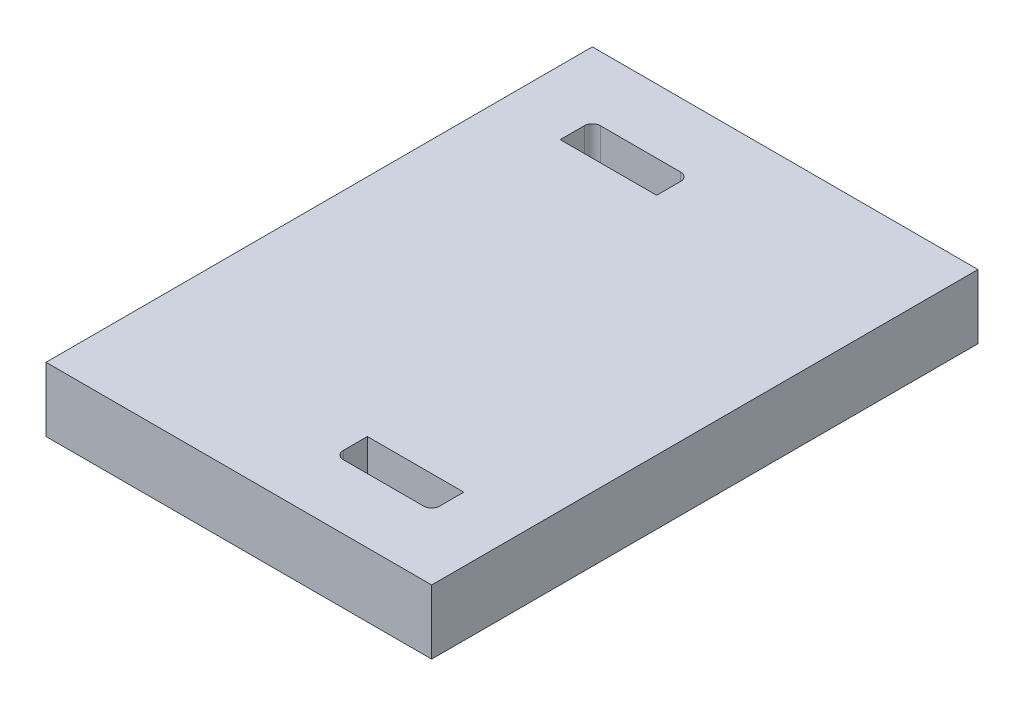
SolidWorks part; units mm, degrees
ref_plane "Ebene vorne" through (0, 0, 0) normal (0, 0, 1) x (1, 0, 0)
ref_plane "Ebene oben" through (0, 0, 0) normal (0, 1, 0) x (1, 0, 0)
ref_plane "Ebene rechts" through (0, 0, 0) normal (1, 0, 0) x (0, 0, -1)
sketch "Skizze1" plane through (0, 0, 0) normal (0, 1, 0) x (1, 0, 0)
  line L1 (0, 0) -> (12, 0)
  line L2 (0, 0) -> (0, 17)
  line L3 (0, 17) -> (12, 17)
  line L4 (12, 0) -> (12, 17)
  dimension "D1" = 17
  dimension "D2" = 12
extrude "Aufsatz-Linear austragen1" add sketch "Skizze1" along normal blind 2 contours L2 L3 L4 L1
sketch "Skizze2" plane through (0, 2, 0) normal (0, 1, 0) x (1, 0, 0)
  line L0 (0, 0) -> (0, 17) construction
  line L1 (10, 15) -> (2, 15)
  line L2 (10, 15) -> (10, 2)
  line L3 (10, 2) -> (2, 2)
  line L4 (2, 15) -> (2, 2)
  line L5 (0, 0) -> (12, 0) construction
  dimension "D1" = 13
  dimension "D2" = 2
  dimension "D3" = 2
  dimension "D4" = 8
sketch "Skizze3" plane through (0, 2, 0) normal (0, 1, 0) x (1, 0, 0)
  line L1 (2, 15) -> (5, 15)
  line L2 (2, 15) -> (2, 14)
  line L3 (2, 14) -> (5, 14)
  line L4 (5, 15) -> (5, 14)
  line L5 (10, 2) -> (7, 2)
  line L6 (10, 2) -> (10, 3)
  line L7 (10, 3) -> (7, 3)
  line L8 (7, 2) -> (7, 3)
  dimension "D1" = 1
  dimension "D2" = 3
  dimension "D3" = 1
  dimension "D4" = 3
extrude "Schnitt-Linear austragen1" cut sketch "Skizze3" against normal through all contours L8 L5 L6 L7 | L4 L3 L2 L1
fillet "Verrundung1" radius 0.25 4 edges at (7, 1, -2) (10, 1, -2) (5, 1, -15) (2, 1, -15)
